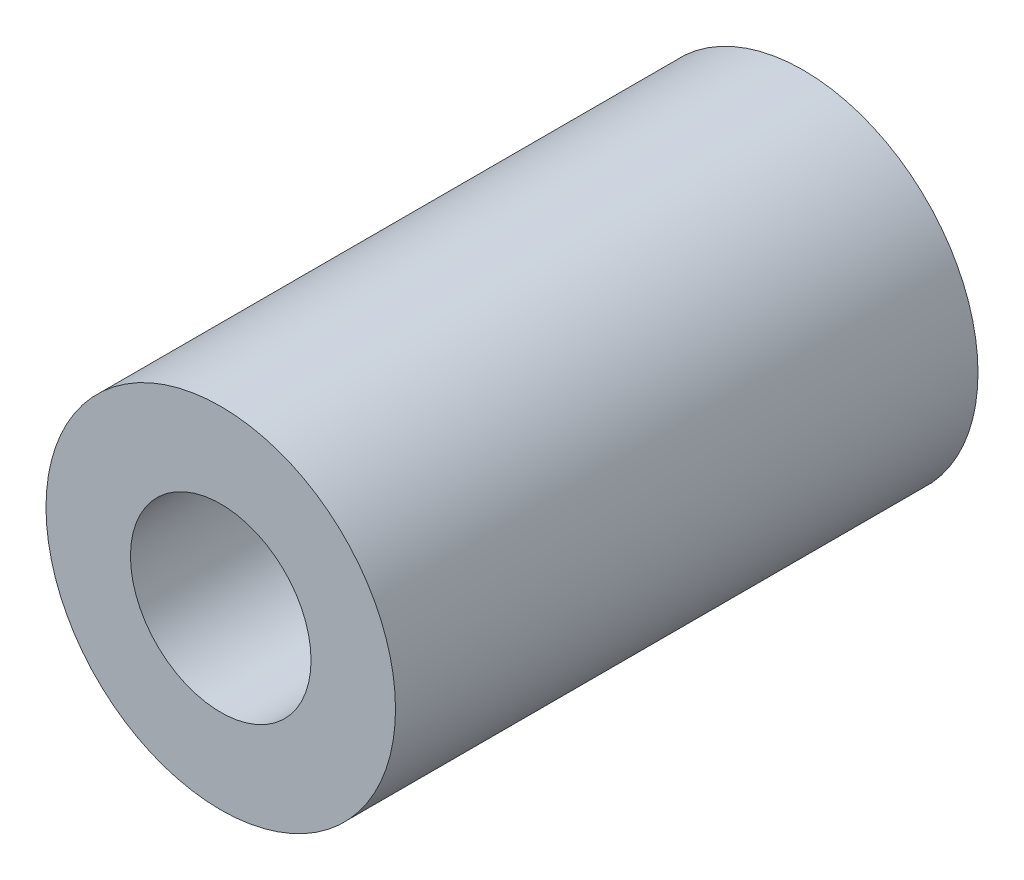
SolidWorks part; units mm, degrees
ref_plane "Plan de face" through (0, 0, 0) normal (0, 0, 1) x (1, 0, 0)
ref_plane "Plan de dessus" through (0, 0, 0) normal (0, 1, 0) x (1, 0, 0)
ref_plane "Plan de droite" through (0, 0, 0) normal (1, 0, 0) x (0, 0, -1)
sketch "Esquisse1" plane through (0, 0, 0) normal (0, 0, 1) x (1, 0, 0)
  circle A0 centre (0, 0) radius 3
  circle A1 centre (0, 0) radius 1.55
extrude "Extrusion1" add sketch "Esquisse1" along normal blind 10
